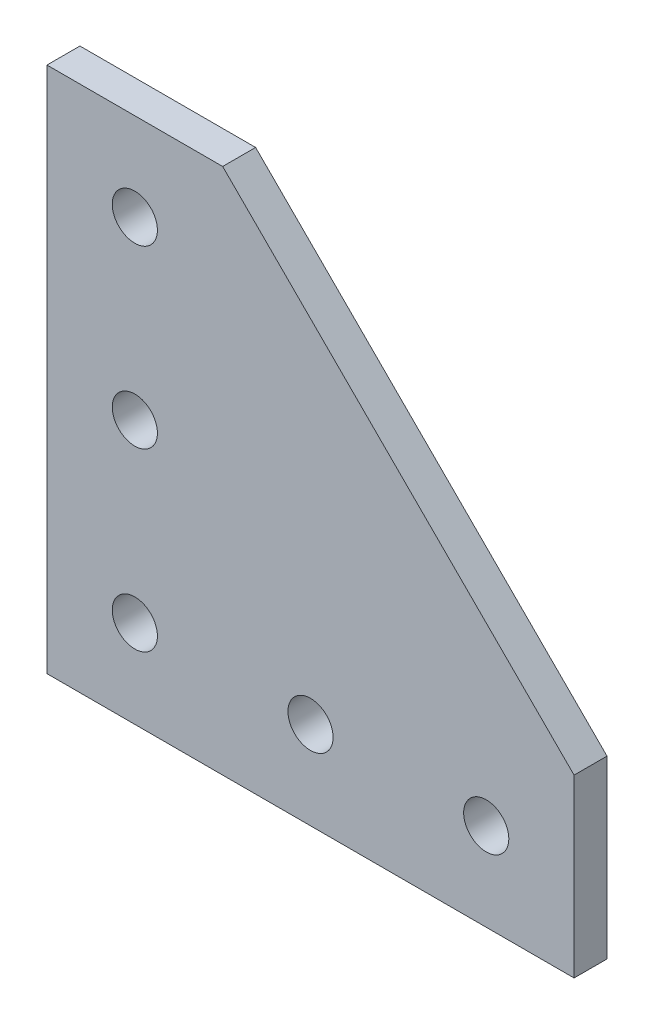
SolidWorks part; units mm, degrees
ref_plane "Front Plane" through (0, 0, 0) normal (0, 0, 1) x (1, 0, 0)
ref_plane "Top Plane" through (0, 0, 0) normal (0, 1, 0) x (1, 0, 0)
ref_plane "Right Plane" through (0, 0, 0) normal (1, 0, 0) x (0, 0, -1)
sketch "Sketch1" plane through (0, 0, 0) normal (0, 0, 1) x (1, 0, 0)
  line L0 (0, 0) -> (0, 76.2)
  line L1 (12.7, 12.7) -> (38.1, 12.7) construction
  line L2 (38.1, 12.7) -> (63.5, 12.7) construction
  line L3 (12.7, 12.7) -> (12.7, 38.1) construction
  line L4 (76.2, 25.4) -> (25.4, 76.2)
  line L5 (76.2, 0) -> (0, 0)
  line L6 (12.7, 38.1) -> (12.7, 63.5) construction
  line L7 (76.2, 25.4) -> (76.2, 0)
  line L8 (0, 76.2) -> (25.4, 76.2)
  circle A0 centre (12.7, 12.7) radius 3.2639
  circle A1 centre (38.1, 12.7) radius 3.2639
  circle A2 centre (63.5, 12.7) radius 3.2639
  circle A3 centre (12.7, 38.1) radius 3.2639
  circle A4 centre (12.7, 63.5) radius 3.2639
  dimension "D1" = 25.4
  dimension "E" = 6.5278
  dimension "D2" = 12.7
  dimension "C" = 25.4
  dimension "D3" = 12.7
  dimension "B" = 76.2
extrude "Boss-Extrude1" add sketch "Sketch1" along normal mid plane 4.7625
